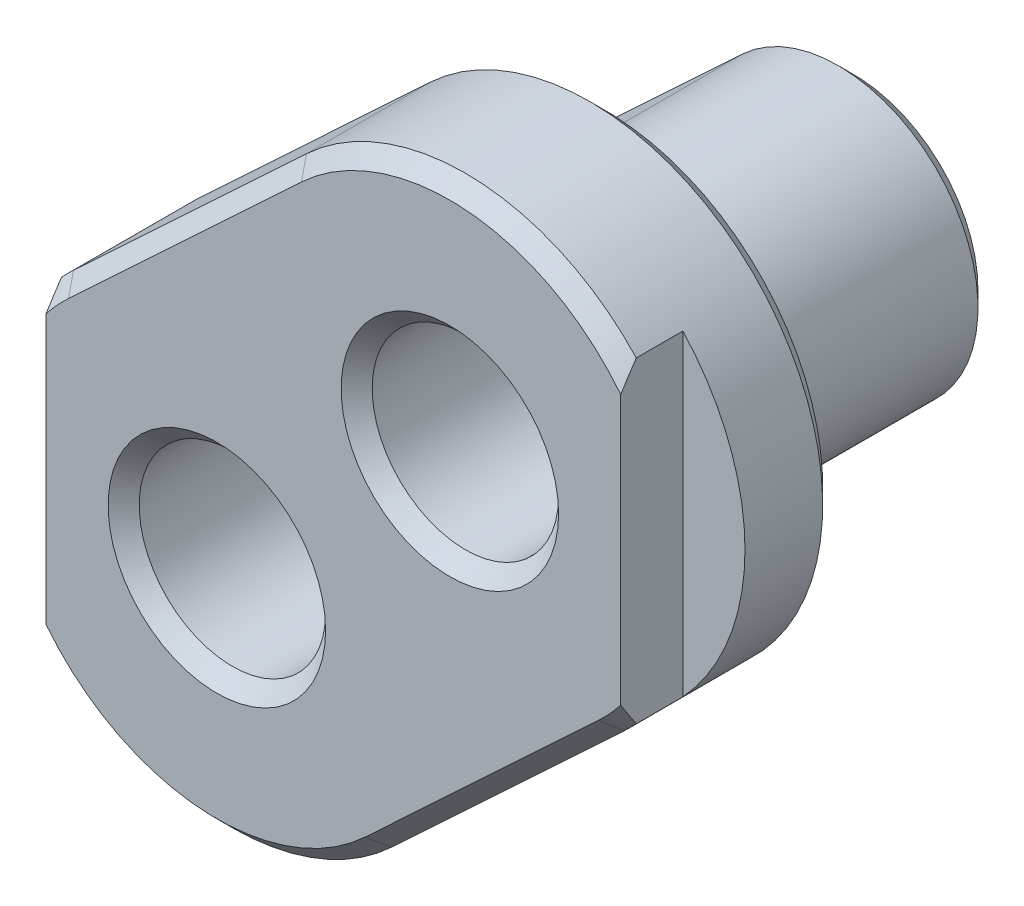
SolidWorks part; units mm, degrees
material "AISI 1020 钢，冷轧"
ref_plane "前视基准面" through (0, 0, 0) normal (0, 0, 1) x (1, 0, 0)
ref_plane "上视基准面" through (0, 0, 0) normal (0, 1, 0) x (1, 0, 0)
ref_plane "右视基准面" through (0, 0, 0) normal (1, 0, 0) x (0, 0, -1)
sketch "草图1" plane through (0, 0, 0) normal (0, 0, 1) x (1, 0, 0)
  line L2 (6.1409, -6.5795) -> (21.1409, 7.4205)
  line L3 (8.8591, 20.5795) -> (-6.1409, 6.5795)
  line L4 (0, 0) -> (15, 0) construction
  line L5 (15, 14) -> (15, 0) construction
  line L6 (15, 14) -> (0, 0) construction
  arc A2 (21.1409, 7.4205) -> (8.8591, 20.5795) centre (15, 14) ccw
  arc A3 (-6.1409, 6.5795) -> (6.1409, -6.5795) centre (0, 0) ccw
  dimension "D3" = 9
  dimension "D4" = 9
  dimension "D1" = 14
  dimension "D2" = 15
extrude "凸台-拉伸1" add sketch "草图1" along normal blind 16
sketch "草图2" plane through (0, 0, 16) normal (0, 0, 1) x (1, 0, 0)
  line L4 (10.2348, -10.9658) -> (25.2348, 3.0342)
  line L5 (4.7652, 24.9658) -> (-10.2348, 10.9658)
  line L6 (10.2348, -10.9658) -> (25.2348, 3.0342)
  line L7 (4.7652, 24.9658) -> (-10.2348, 10.9658)
  arc A4 (-10.2348, 10.9658) -> (10.2348, -10.9658) centre (0, 0) ccw
  arc A5 (25.2348, 3.0342) -> (4.7652, 24.9658) centre (15, 14) ccw
  arc A6 (-10.2348, 10.9658) -> (10.2348, -10.9658) centre (0, 0) ccw
  arc A7 (25.2348, 3.0342) -> (4.7652, 24.9658) centre (15, 14) ccw
  dimension "D1" = 6
extrude "凸台-拉伸2" add sketch "草图2" along normal blind 10
sketch "草图3" plane through (0, 0, 26) normal (0, 0, 1) x (1, 0, 0)
  line L0 (26, 24.198) -> (26, 3.802)
  line L1 (-11, 10.198) -> (-11, -10.198)
  line L2 (10.2348, -10.9658) -> (25.2348, 3.0342)
  line L3 (4.7652, 24.9658) -> (-10.2348, 10.9658)
  arc A2 (-10.2348, 10.9658) -> (10.2348, -10.9658) centre (0, 0) ccw
  arc A3 (25.2348, 3.0342) -> (4.7652, 24.9658) centre (15, 14) ccw
  arc A4 (-11, 10.198) -> (-11, -10.198) centre (0, 0) ccw
  arc A5 (26, 3.802) -> (26, 24.198) centre (15, 14) ccw
  dimension "D2" = 11
  dimension "D3" = 11
  dimension "D1" = 0
extrude "切除-拉伸1" cut sketch "草图3" against normal blind 4
sketch "草图4" plane through (0, 0, 0) normal (0, 0, -1) x (-1, 0, 0)
  circle A0 centre (0, 0) radius 6
  circle A1 centre (-15, 14) radius 6
  dimension "D1" = 12
  dimension "D2" = 12
extrude "切除-拉伸2" cut sketch "草图4" against normal through all contours A1
chamfer "倒角1" distance 1 angle 45 18 edges at (13.6409, 0.4205, 0) (21.5795, 20.1409, 0) (1.3591, 13.5795, 0) (-6.5795, -6.1409, 0) (9, 14, 0) (-6, 0, 0) (-2.7348, 17.9658, 16) (-10.9658, -10.2348, 16) (25.9658, 24.2348, 16) (17.7348, -3.9658, 16) (9, 14, 26) (-6, 0, 26) (25.6243, 3.4112, 26) (17.7348, -3.9658, 26) (-0.542, -14.9902, 26) (-10.6243, 10.5888, 26) (-2.7348, 17.9658, 26) (15.542, 28.9902, 26)
